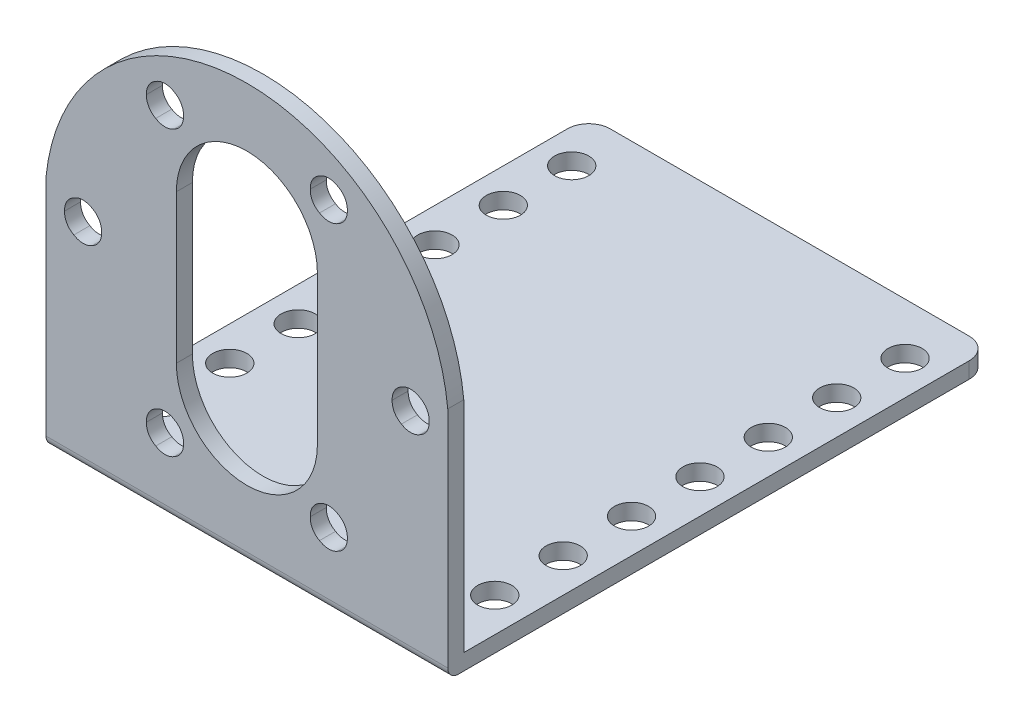
SolidWorks part; units mm, degrees
ref_plane "Front Plane" through (0, 0, 0) normal (0, 0, 1) x (1, 0, 0)
ref_plane "Top Plane" through (0, 0, 0) normal (0, 1, 0) x (1, 0, 0)
ref_plane "Right Plane" through (0, 0, 0) normal (1, 0, 0) x (0, 0, -1)
sketch "Sketch1" plane through (0, 0, 0) normal (0, 0, 1) x (1, 0, 0)
  line L0 (0, 0) -> (0, 39) construction
  line L1 (-18.8, 0) -> (18.8, 0)
  line L2 (-18.8, 0) -> (-18.8, 22)
  line L4 (18.8, 0) -> (18.8, 22)
  line L6 (-6.6, 12.9994) -> (-6.6, 26.8994)
  line L8 (6.6, 12.9994) -> (6.6, 26.8994)
  arc A0 (-18.8, 22) -> (18.8, 22) centre (0, 20.1047) cw
  arc A1 (-6.6, 26.8994) -> (6.6, 26.8994) centre (0, 26.9) cw
  arc A2 (-6.6, 12.9994) -> (6.6, 12.9994) centre (0, 13) ccw
  dimension "D3" = 39
  dimension "D5" = 27.1
  dimension "D6" = 5.5
  dimension "D1" = 37.6
  dimension "D2" = 22
  dimension "D4" = 13.2
  dimension "D7" = 13.9
extrude "Boss-Extrude1" add sketch "Sketch1" along normal blind 1.5
sketch "Sketch2" plane through (0, 0, 0) normal (0, -1, 0) x (1, 0, 0)
  line L0 (18.8, 1.5) -> (18.8, 0) construction
  line L1 (-18.8, 1.5) -> (18.8, 1.5)
  line L2 (-18.8, 1.5) -> (-18.8, -49.3)
  line L3 (-18.8, -49.3) -> (18.8, -49.3)
  line L4 (18.8, 1.5) -> (18.8, -49.3)
  dimension "D1" = 50.8
extrude "Boss-Extrude2" add sketch "Sketch2" against normal blind 1.5
fillet "Fillet1" radius 1 1 edges at (0, 0, 1.5)
fillet "Fillet2" radius 2 2 edges at (-18.8, 0.75, -49.3) (18.8, 0.75, -49.3)
sketch "Sketch3" plane through (0, 0, 0) normal (0, -1, 0) x (1, 0, 0)
  line L0 (-16.8, -49.3) -> (16.8, -49.3) construction
  line L1 (-18.8, 0.5) -> (-18.8, -47.3) construction
  circle A0 centre (-15.6, -44.5) radius 1.6
  dimension "D1" = 3.2
  dimension "D2" = 4.8
  dimension "D3" = 3.2
extrude "Cut-Extrude1" cut sketch "Sketch3" against normal up to next (1.5 mm away)
pattern_linear "LPattern1" count 7 spacing 6.4 along (0, 0, 1) of "Cut-Extrude1"
mirror "Mirror1" about plane through (0, 0, 0) normal (1, 0, 0) of "LPattern1", "Cut-Extrude1"
sketch "Sketch4" plane through (0, 0, 1.5) normal (0, 0, 1) x (1, 0, 0)
  line L0 (0, 0) -> (0, 39) construction
  line L1 (-7.6648, 33.2258) -> (-5.815, 30.0218) construction
  line L2 (-5.815, 30.0218) -> (0, 19.95) construction
  line L3 (0, 19.95) -> (-5.815, 9.8782) construction
  line L4 (0, 19.95) -> (5.815, 9.8782) construction
  line L5 (5.815, 9.8782) -> (7.6648, 6.6742) construction
  line L6 (0, 19.95) -> (5.815, 30.0218) construction
  line L7 (5.815, 30.0218) -> (7.6648, 33.2258) construction
  line L8 (-5.815, 9.8782) -> (-7.6648, 6.6742) construction
  line L9 (7.325, 33.2258) -> (7.6648, 33.2258) construction
  line L10 (7.6648, 33.2258) -> (9.5146, 36.4297) construction
  circle A0 centre (7.6648, 33.2258) radius 1.6
  arc A1 (18.8, 22) -> (-18.8, 22) centre (0, 20.1047) ccw construction
  circle A3 centre (15.3295, 19.95) radius 1.6
  circle A4 centre (7.6648, 6.6742) radius 1.6
  circle A5 centre (-7.6648, 6.6742) radius 1.6
  circle A6 centre (-15.3295, 19.95) radius 1.6
  circle A7 centre (-7.6648, 33.2258) radius 1.6
  arc A8 (-6.6, 12.9994) -> (6.6, 12.9994) centre (0, 13) ccw construction
  arc A9 (6.6, 26.8994) -> (-6.6, 26.8994) centre (0, 26.9) ccw construction
  point P26 (0, 19.95)
  dimension "D1" = 3.2
  dimension "D2" = 6
extrude "Cut-Extrude2" cut sketch "Sketch4" against normal up to next (1.5 mm away)
pattern_circular "CirPattern1" count 6 over 360 about axis through (0, 20.1047, 0) along (0, 0, 1) of "Cut-Extrude2"
